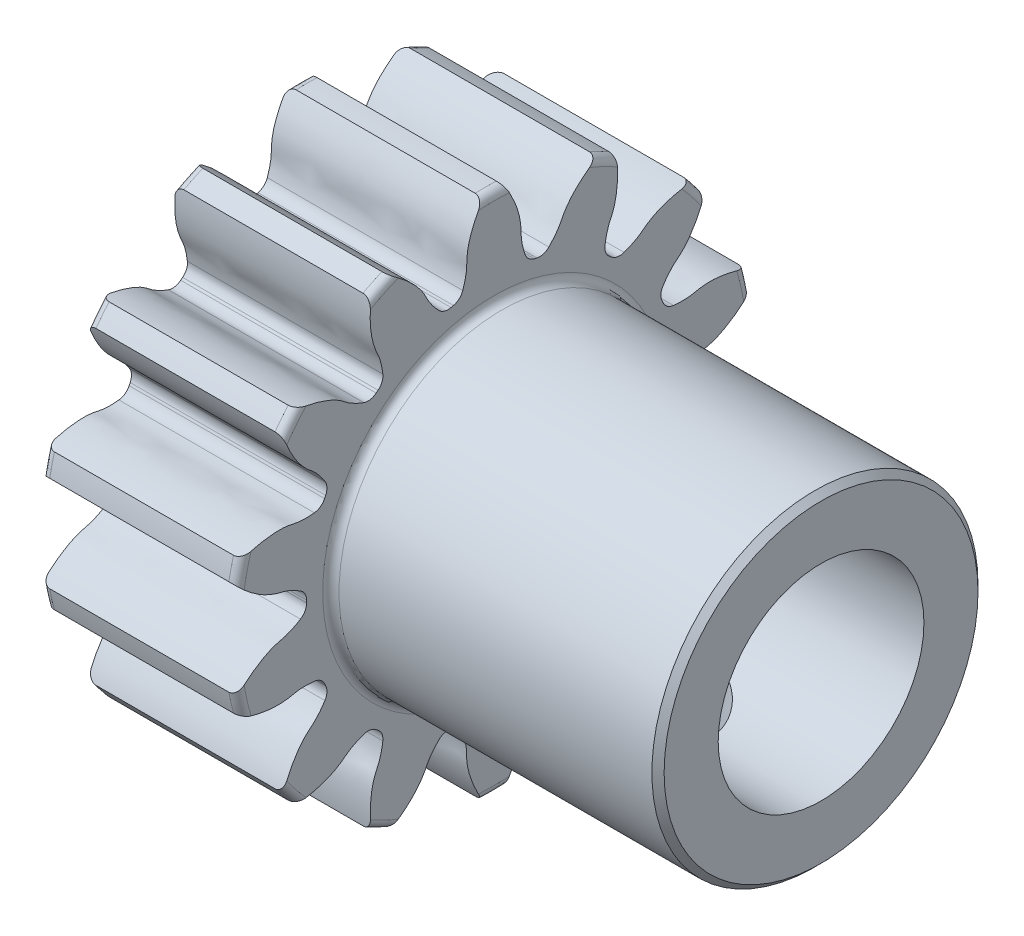
SolidWorks part; units mm, degrees
ref_plane "Front Plane" through (0, 0, 0) normal (0, 0, 1) x (1, 0, 0)
ref_plane "Top Plane" through (0, 0, 0) normal (0, 1, 0) x (1, 0, 0)
ref_plane "Right Plane" through (0, 0, 0) normal (1, 0, 0) x (0, 0, -1)
sketch "Sketch1" plane through (0, 0, 0) normal (0, 0, 1) x (1, 0, 0)
  line L0 (-2.3749, 6.35) -> (-2.3749, 0)
  line L1 (-2.3749, 0) -> (2.3749, 0)
  line L2 (2.3749, 0) -> (2.3749, 6.35)
  line L3 (2.3749, 6.35) -> (-2.3749, 6.35)
  line L4 (-2.3749, 0) -> (2.3749, 0) construction
revolve "Revolve1" add sketch "Sketch1" angle 360 about L4
sketch "Sketch2" plane through (2.3749, 0, 0) normal (1, 0, 0) x (0, 0, -1)
  arc A0 (2.522, 5.8277) -> (0.2563, 6.3448) centre (0, 0) ccw
  arc A1 (0.8169, 4.4791) -> (1.2074, 4.3899) centre (0, 0) cw
  spline S0 degree 3 poles (0.8169, 4.4791) (0.7969, 4.5356) (0.7764, 4.592) (0.7572, 4.6489) (0.7045, 4.8054) (0.6603, 4.9699) (0.6613, 5.1352) (0.6623, 5.3039) (0.6386, 5.4749) (0.5897, 5.6364) (0.537, 5.8109) (0.4638, 5.9799) (0.3768, 6.14) (0.339, 6.2096) (0.2987, 6.2779) (0.2563, 6.3448) knots -0.000178 -0.000178 -0.000178 -0.000178 0 0 0 0.000496 0.000496 0.000496 0.000997 0.000997 0.000997 0.001536 0.001536 0.001536 0.001769 0.001769 0.001769 0.001769
  spline S1 degree 3 poles (1.2074, 4.3899) (1.25, 4.4322) (1.2929, 4.4741) (1.3348, 4.517) (1.4503, 4.6352) (1.5615, 4.7642) (1.6323, 4.9135) (1.7046, 5.066) (1.8001, 5.2098) (1.9142, 5.3341) (2.0375, 5.4684) (2.1767, 5.5889) (2.3246, 5.6954) (2.3888, 5.7418) (2.4548, 5.7858) (2.522, 5.8277) knots -0.000178 -0.000178 -0.000178 -0.000178 0 0 0 0.000496 0.000496 0.000496 0.000997 0.000997 0.000997 0.001536 0.001536 0.001536 0.001769 0.001769 0.001769 0.001769
extrude "Cut-Extrude1" cut sketch "Sketch2" against normal through all
sketch "Sketch3" plane through (2.3749, 0, 0) normal (1, 0, 0) x (0, 0, -1)
  arc A0 (4.8008, 4.1563) -> (2.9838, 5.6053) centre (0, 0) ccw
  arc A1 (2.6794, 3.6811) -> (2.9926, 3.4313) centre (0, 0) cw
  spline S0 degree 3 poles (2.9838, 5.6053) (2.993, 5.5266) (2.9997, 5.4476) (3.0035, 5.3685) (3.0144, 5.1469) (2.9998, 4.9222) (2.9558, 4.7048) (2.9338, 4.596) (2.8984, 4.4887) (2.8487, 4.3895) (2.7829, 4.2582) (2.7401, 4.1143) (2.7155, 3.9695) (2.7093, 3.9331) (2.7039, 3.8966) (2.6993, 3.8599) (2.6919, 3.8004) (2.6859, 3.7407) (2.6794, 3.6811) knots -0.000236 -0.000236 -0.000236 -0.000236 0 0 0 0.000665 0.000665 0.000665 0.000998 0.000998 0.000998 0.00144 0.00144 0.00144 0.00155 0.00155 0.00155 0.001729 0.001729 0.001729 0.001729
  spline S1 degree 3 poles (2.9926, 3.4313) (3.0492, 3.451) (3.1061, 3.4701) (3.1625, 3.4905) (3.3178, 3.5469) (3.474, 3.6149) (3.6025, 3.7187) (3.7339, 3.8248) (3.8823, 3.9128) (4.0391, 3.9753) (4.2083, 4.0428) (4.3861, 4.091) (4.5655, 4.1228) (4.6435, 4.1367) (4.722, 4.1477) (4.8008, 4.1563) knots -0.000178 -0.000178 -0.000178 -0.000178 0 0 0 0.000496 0.000496 0.000496 0.000997 0.000997 0.000997 0.001536 0.001536 0.001536 0.001769 0.001769 0.001769 0.001769
extrude "Cut-Extrude2" cut sketch "Sketch3" against normal through all
sketch "Sketch4" plane through (2.3749, 0, 0) normal (1, 0, 0) x (0, 0, -1)
  arc A0 (6.1287, 1.6617) -> (5.1204, 3.7555) centre (0, 0) ccw
  arc A1 (4.0112, 2.154) -> (4.185, 1.7931) centre (0, 0) cw
  spline S0 degree 3 poles (5.1204, 3.7555) (5.0945, 3.6807) (5.0662, 3.6066) (5.0354, 3.5336) (4.949, 3.3293) (4.8383, 3.1332) (4.7044, 2.9564) (4.6374, 2.8679) (4.5589, 2.7866) (4.4711, 2.7188) (4.3548, 2.629) (4.2538, 2.518) (4.1688, 2.3982) (4.1475, 2.3681) (4.1268, 2.3375) (4.1068, 2.3065) (4.0742, 2.2561) (4.043, 2.2049) (4.0112, 2.154) knots -0.000236 -0.000236 -0.000236 -0.000236 0 0 0 0.000665 0.000665 0.000665 0.000998 0.000998 0.000998 0.00144 0.00144 0.00144 0.00155 0.00155 0.00155 0.001729 0.001729 0.001729 0.001729
  spline S1 degree 3 poles (4.185, 1.7931) (4.2446, 1.7862) (4.3041, 1.7787) (4.3638, 1.7727) (4.5282, 1.7561) (4.6984, 1.7496) (4.8593, 1.7874) (5.0236, 1.8259) (5.1955, 1.8408) (5.3639, 1.8292) (5.5457, 1.8165) (5.7267, 1.7828) (5.9022, 1.7336) (5.9785, 1.7123) (6.054, 1.6881) (6.1287, 1.6617) knots -0.000178 -0.000178 -0.000178 -0.000178 0 0 0 0.000496 0.000496 0.000496 0.000997 0.000997 0.000997 0.001536 0.001536 0.001536 0.001769 0.001769 0.001769 0.001769
extrude "Cut-Extrude3" cut sketch "Sketch4" against normal through all
sketch "Sketch5" plane through (2.3749, 0, 0) normal (1, 0, 0) x (0, 0, -1)
  arc A0 (6.2428, -1.162) -> (6.2428, 1.162) centre (0, 0) ccw
  arc A1 (4.5485, 0.2003) -> (4.5485, -0.2003) centre (0, 0) cw
  spline S0 degree 3 poles (6.2428, 1.162) (6.187, 1.1058) (6.1294, 1.0513) (6.0699, 0.9989) (5.9035, 0.8523) (5.7186, 0.7236) (5.5213, 0.6225) (5.4225, 0.5718) (5.3165, 0.5326) (5.2079, 0.5096) (5.0643, 0.4792) (4.9251, 0.4229) (4.7965, 0.3519) (4.7642, 0.334) (4.7323, 0.3155) (4.7008, 0.2962) (4.6496, 0.2649) (4.5993, 0.2323) (4.5485, 0.2003) knots -0.000236 -0.000236 -0.000236 -0.000236 0 0 0 0.000665 0.000665 0.000665 0.000998 0.000998 0.000998 0.00144 0.00144 0.00144 0.00155 0.00155 0.00155 0.001729 0.001729 0.001729 0.001729
  spline S1 degree 3 poles (4.5485, -0.2003) (4.5993, -0.2323) (4.6496, -0.2649) (4.7008, -0.2962) (4.8417, -0.3825) (4.9923, -0.4622) (5.1536, -0.498) (5.3183, -0.5345) (5.4797, -0.5957) (5.6263, -0.6793) (5.7847, -0.7695) (5.9331, -0.8785) (6.0699, -0.9989) (6.1294, -1.0513) (6.187, -1.1058) (6.2428, -1.162) knots -0.000178 -0.000178 -0.000178 -0.000178 0 0 0 0.000496 0.000496 0.000496 0.000997 0.000997 0.000997 0.001536 0.001536 0.001536 0.001769 0.001769 0.001769 0.001769
extrude "Cut-Extrude4" cut sketch "Sketch5" against normal through all
sketch "Sketch6" plane through (2.3749, 0, 0) normal (1, 0, 0) x (0, 0, -1)
  arc A0 (5.1204, -3.7555) -> (6.1287, -1.6617) centre (0, 0) ccw
  arc A1 (4.185, -1.7931) -> (4.0112, -2.154) centre (0, 0) cw
  spline S0 degree 3 poles (6.1287, -1.6617) (6.054, -1.6881) (5.9785, -1.7123) (5.9022, -1.7336) (5.6886, -1.7935) (5.4663, -1.8293) (5.2446, -1.8348) (5.1336, -1.8375) (5.0211, -1.8269) (4.9133, -1.8005) (4.7707, -1.7656) (4.6208, -1.7559) (4.4742, -1.7641) (4.4374, -1.7662) (4.4005, -1.769) (4.3638, -1.7727) (4.3041, -1.7787) (4.2446, -1.7862) (4.185, -1.7931) knots -0.000236 -0.000236 -0.000236 -0.000236 0 0 0 0.000665 0.000665 0.000665 0.000998 0.000998 0.000998 0.00144 0.00144 0.00144 0.00155 0.00155 0.00155 0.001729 0.001729 0.001729 0.001729
  spline S1 degree 3 poles (4.0112, -2.154) (4.043, -2.2049) (4.0742, -2.2561) (4.1068, -2.3065) (4.1963, -2.4454) (4.2973, -2.5825) (4.4271, -2.6847) (4.5597, -2.7892) (4.6786, -2.9143) (4.7744, -3.0532) (4.8779, -3.2032) (4.9644, -3.3658) (5.0354, -3.5336) (5.0662, -3.6066) (5.0945, -3.6807) (5.1204, -3.7555) knots -0.000178 -0.000178 -0.000178 -0.000178 0 0 0 0.000496 0.000496 0.000496 0.000997 0.000997 0.000997 0.001536 0.001536 0.001536 0.001769 0.001769 0.001769 0.001769
extrude "Cut-Extrude5" cut sketch "Sketch6" against normal through all
sketch "Sketch7" plane through (2.3749, 0, 0) normal (1, 0, 0) x (0, 0, -1)
  arc A0 (2.9838, -5.6053) -> (4.8008, -4.1563) centre (0, 0) ccw
  arc A1 (2.9926, -3.4313) -> (2.6794, -3.6811) centre (0, 0) cw
  spline S0 degree 3 poles (4.8008, -4.1563) (4.722, -4.1477) (4.6435, -4.1367) (4.5655, -4.1228) (4.3471, -4.0841) (4.1313, -4.0198) (3.9291, -3.9286) (3.8279, -3.8829) (3.7312, -3.8246) (3.6455, -3.754) (3.5322, -3.6606) (3.4014, -3.5869) (3.2657, -3.5307) (3.2316, -3.5166) (3.1972, -3.5031) (3.1625, -3.4905) (3.1061, -3.4701) (3.0492, -3.451) (2.9926, -3.4313) knots -0.000236 -0.000236 -0.000236 -0.000236 0 0 0 0.000665 0.000665 0.000665 0.000998 0.000998 0.000998 0.00144 0.00144 0.00144 0.00155 0.00155 0.00155 0.001729 0.001729 0.001729 0.001729
  spline S1 degree 3 poles (2.6794, -3.6811) (2.6859, -3.7407) (2.6919, -3.8004) (2.6993, -3.8599) (2.7197, -4.0239) (2.7513, -4.1913) (2.8239, -4.3397) (2.898, -4.4913) (2.9508, -4.6556) (2.9769, -4.8224) (3.005, -5.0024) (3.0124, -5.1864) (3.0035, -5.3685) (2.9997, -5.4476) (2.993, -5.5266) (2.9838, -5.6053) knots -0.000178 -0.000178 -0.000178 -0.000178 0 0 0 0.000496 0.000496 0.000496 0.000997 0.000997 0.000997 0.001536 0.001536 0.001536 0.001769 0.001769 0.001769 0.001769
extrude "Cut-Extrude6" cut sketch "Sketch7" against normal through all
sketch "Sketch8" plane through (2.3749, 0, 0) normal (1, 0, 0) x (0, 0, -1)
  arc A0 (0.2563, -6.3448) -> (2.522, -5.8277) centre (0, 0) ccw
  arc A1 (1.2074, -4.3899) -> (0.8169, -4.4791) centre (0, 0) cw
  spline S0 degree 3 poles (2.522, -5.8277) (2.4548, -5.7858) (2.3888, -5.7418) (2.3246, -5.6954) (2.1446, -5.5658) (1.978, -5.4142) (1.8354, -5.2443) (1.7641, -5.1593) (1.7023, -5.0647) (1.6557, -4.964) (1.5941, -4.8307) (1.5083, -4.7075) (1.4104, -4.598) (1.3858, -4.5704) (1.3606, -4.5434) (1.3348, -4.517) (1.2929, -4.4741) (1.25, -4.4322) (1.2074, -4.3899) knots -0.000236 -0.000236 -0.000236 -0.000236 0 0 0 0.000665 0.000665 0.000665 0.000998 0.000998 0.000998 0.00144 0.00144 0.00144 0.00155 0.00155 0.00155 0.001729 0.001729 0.001729 0.001729
  spline S1 degree 3 poles (0.8169, -4.4791) (0.7969, -4.5356) (0.7764, -4.592) (0.7572, -4.6489) (0.7045, -4.8054) (0.6603, -4.9699) (0.6613, -5.1352) (0.6623, -5.3039) (0.6386, -5.4749) (0.5897, -5.6364) (0.537, -5.8109) (0.4638, -5.9799) (0.3768, -6.14) (0.339, -6.2096) (0.2987, -6.2779) (0.2563, -6.3448) knots -0.000178 -0.000178 -0.000178 -0.000178 0 0 0 0.000496 0.000496 0.000496 0.000997 0.000997 0.000997 0.001536 0.001536 0.001536 0.001769 0.001769 0.001769 0.001769
extrude "Cut-Extrude7" cut sketch "Sketch8" against normal through all
sketch "Sketch9" plane through (2.3749, 0, 0) normal (1, 0, 0) x (0, 0, -1)
  arc A0 (-2.522, -5.8277) -> (-0.2563, -6.3448) centre (0, 0) ccw
  arc A1 (-0.8169, -4.4791) -> (-1.2074, -4.3899) centre (0, 0) cw
  spline S0 degree 3 poles (-0.2563, -6.3448) (-0.2987, -6.2779) (-0.339, -6.2096) (-0.3768, -6.14) (-0.4827, -5.9451) (-0.567, -5.7363) (-0.6217, -5.5213) (-0.6491, -5.4138) (-0.6638, -5.3018) (-0.662, -5.1908) (-0.6597, -5.0439) (-0.6836, -4.8957) (-0.7243, -4.7546) (-0.7345, -4.7191) (-0.7454, -4.6838) (-0.7572, -4.6489) (-0.7764, -4.592) (-0.7969, -4.5356) (-0.8169, -4.4791) knots -0.000236 -0.000236 -0.000236 -0.000236 0 0 0 0.000665 0.000665 0.000665 0.000998 0.000998 0.000998 0.00144 0.00144 0.00144 0.00155 0.00155 0.00155 0.001729 0.001729 0.001729 0.001729
  spline S1 degree 3 poles (-1.2074, -4.3899) (-1.25, -4.4322) (-1.2929, -4.4741) (-1.3348, -4.517) (-1.4503, -4.6352) (-1.5615, -4.7642) (-1.6323, -4.9135) (-1.7046, -5.066) (-1.8001, -5.2098) (-1.9142, -5.3341) (-2.0375, -5.4684) (-2.1767, -5.5889) (-2.3246, -5.6954) (-2.3888, -5.7418) (-2.4548, -5.7858) (-2.522, -5.8277) knots -0.000178 -0.000178 -0.000178 -0.000178 0 0 0 0.000496 0.000496 0.000496 0.000997 0.000997 0.000997 0.001536 0.001536 0.001536 0.001769 0.001769 0.001769 0.001769
extrude "Cut-Extrude8" cut sketch "Sketch9" against normal through all
sketch "Sketch10" plane through (2.3749, 0, 0) normal (1, 0, 0) x (0, 0, -1)
  arc A0 (-4.8008, -4.1563) -> (-2.9838, -5.6053) centre (0, 0) ccw
  arc A1 (-2.6794, -3.6811) -> (-2.9926, -3.4313) centre (0, 0) cw
  spline S0 degree 3 poles (-2.9838, -5.6053) (-2.993, -5.5266) (-2.9997, -5.4476) (-3.0035, -5.3685) (-3.0144, -5.1469) (-2.9998, -4.9222) (-2.9558, -4.7048) (-2.9338, -4.596) (-2.8984, -4.4887) (-2.8487, -4.3895) (-2.7829, -4.2582) (-2.7401, -4.1143) (-2.7155, -3.9695) (-2.7093, -3.9331) (-2.7039, -3.8966) (-2.6993, -3.8599) (-2.6919, -3.8004) (-2.6859, -3.7407) (-2.6794, -3.6811) knots -0.000236 -0.000236 -0.000236 -0.000236 0 0 0 0.000665 0.000665 0.000665 0.000998 0.000998 0.000998 0.00144 0.00144 0.00144 0.00155 0.00155 0.00155 0.001729 0.001729 0.001729 0.001729
  spline S1 degree 3 poles (-2.9926, -3.4313) (-3.0492, -3.451) (-3.1061, -3.4701) (-3.1625, -3.4905) (-3.3178, -3.5469) (-3.474, -3.6149) (-3.6025, -3.7187) (-3.7339, -3.8248) (-3.8823, -3.9128) (-4.0391, -3.9753) (-4.2083, -4.0428) (-4.3861, -4.091) (-4.5655, -4.1228) (-4.6435, -4.1367) (-4.722, -4.1477) (-4.8008, -4.1563) knots -0.000178 -0.000178 -0.000178 -0.000178 0 0 0 0.000496 0.000496 0.000496 0.000997 0.000997 0.000997 0.001536 0.001536 0.001536 0.001769 0.001769 0.001769 0.001769
extrude "Cut-Extrude9" cut sketch "Sketch10" against normal through all
sketch "Sketch11" plane through (2.3749, 0, 0) normal (1, 0, 0) x (0, 0, -1)
  arc A0 (-6.1287, -1.6617) -> (-5.1204, -3.7555) centre (0, 0) ccw
  arc A1 (-4.0112, -2.154) -> (-4.185, -1.7931) centre (0, 0) cw
  spline S0 degree 3 poles (-5.1204, -3.7555) (-5.0945, -3.6807) (-5.0662, -3.6066) (-5.0354, -3.5336) (-4.949, -3.3293) (-4.8383, -3.1332) (-4.7044, -2.9564) (-4.6374, -2.8679) (-4.5589, -2.7866) (-4.4711, -2.7188) (-4.3548, -2.629) (-4.2538, -2.518) (-4.1688, -2.3982) (-4.1475, -2.3681) (-4.1268, -2.3375) (-4.1068, -2.3065) (-4.0742, -2.2561) (-4.043, -2.2049) (-4.0112, -2.154) knots -0.000236 -0.000236 -0.000236 -0.000236 0 0 0 0.000665 0.000665 0.000665 0.000998 0.000998 0.000998 0.00144 0.00144 0.00144 0.00155 0.00155 0.00155 0.001729 0.001729 0.001729 0.001729
  spline S1 degree 3 poles (-4.185, -1.7931) (-4.2446, -1.7862) (-4.3041, -1.7787) (-4.3638, -1.7727) (-4.5282, -1.7561) (-4.6984, -1.7496) (-4.8593, -1.7874) (-5.0236, -1.8259) (-5.1955, -1.8408) (-5.3639, -1.8292) (-5.5457, -1.8165) (-5.7267, -1.7828) (-5.9022, -1.7336) (-5.9785, -1.7123) (-6.054, -1.6881) (-6.1287, -1.6617) knots -0.000178 -0.000178 -0.000178 -0.000178 0 0 0 0.000496 0.000496 0.000496 0.000997 0.000997 0.000997 0.001536 0.001536 0.001536 0.001769 0.001769 0.001769 0.001769
extrude "Cut-Extrude10" cut sketch "Sketch11" against normal through all
sketch "Sketch12" plane through (2.3749, 0, 0) normal (1, 0, 0) x (0, 0, -1)
  arc A0 (-6.2428, 1.162) -> (-6.2428, -1.162) centre (0, 0) ccw
  arc A1 (-4.5485, -0.2003) -> (-4.5485, 0.2003) centre (0, 0) cw
  spline S0 degree 3 poles (-6.2428, -1.162) (-6.187, -1.1058) (-6.1294, -1.0513) (-6.0699, -0.9989) (-5.9035, -0.8523) (-5.7186, -0.7236) (-5.5213, -0.6225) (-5.4225, -0.5718) (-5.3165, -0.5326) (-5.2079, -0.5096) (-5.0643, -0.4792) (-4.9251, -0.4229) (-4.7965, -0.3519) (-4.7642, -0.334) (-4.7323, -0.3155) (-4.7008, -0.2962) (-4.6496, -0.2649) (-4.5993, -0.2323) (-4.5485, -0.2003) knots -0.000236 -0.000236 -0.000236 -0.000236 0 0 0 0.000665 0.000665 0.000665 0.000998 0.000998 0.000998 0.00144 0.00144 0.00144 0.00155 0.00155 0.00155 0.001729 0.001729 0.001729 0.001729
  spline S1 degree 3 poles (-4.5485, 0.2003) (-4.5993, 0.2323) (-4.6496, 0.2649) (-4.7008, 0.2962) (-4.8417, 0.3825) (-4.9923, 0.4622) (-5.1536, 0.498) (-5.3183, 0.5345) (-5.4797, 0.5957) (-5.6263, 0.6793) (-5.7847, 0.7695) (-5.9331, 0.8785) (-6.0699, 0.9989) (-6.1294, 1.0513) (-6.187, 1.1058) (-6.2428, 1.162) knots -0.000178 -0.000178 -0.000178 -0.000178 0 0 0 0.000496 0.000496 0.000496 0.000997 0.000997 0.000997 0.001536 0.001536 0.001536 0.001769 0.001769 0.001769 0.001769
extrude "Cut-Extrude11" cut sketch "Sketch12" against normal through all
sketch "Sketch13" plane through (2.3749, 0, 0) normal (1, 0, 0) x (0, 0, -1)
  arc A0 (-5.1204, 3.7555) -> (-6.1287, 1.6617) centre (0, 0) ccw
  arc A1 (-4.185, 1.7931) -> (-4.0112, 2.154) centre (0, 0) cw
  spline S0 degree 3 poles (-6.1287, 1.6617) (-6.054, 1.6881) (-5.9785, 1.7123) (-5.9022, 1.7336) (-5.6886, 1.7935) (-5.4663, 1.8293) (-5.2446, 1.8348) (-5.1336, 1.8375) (-5.0211, 1.8269) (-4.9133, 1.8005) (-4.7707, 1.7656) (-4.6208, 1.7559) (-4.4742, 1.7641) (-4.4374, 1.7662) (-4.4005, 1.769) (-4.3638, 1.7727) (-4.3041, 1.7787) (-4.2446, 1.7862) (-4.185, 1.7931) knots -0.000236 -0.000236 -0.000236 -0.000236 0 0 0 0.000665 0.000665 0.000665 0.000998 0.000998 0.000998 0.00144 0.00144 0.00144 0.00155 0.00155 0.00155 0.001729 0.001729 0.001729 0.001729
  spline S1 degree 3 poles (-4.0112, 2.154) (-4.043, 2.2049) (-4.0742, 2.2561) (-4.1068, 2.3065) (-4.1963, 2.4454) (-4.2973, 2.5825) (-4.4271, 2.6847) (-4.5597, 2.7892) (-4.6786, 2.9143) (-4.7744, 3.0532) (-4.8779, 3.2032) (-4.9644, 3.3658) (-5.0354, 3.5336) (-5.0662, 3.6066) (-5.0945, 3.6807) (-5.1204, 3.7555) knots -0.000178 -0.000178 -0.000178 -0.000178 0 0 0 0.000496 0.000496 0.000496 0.000997 0.000997 0.000997 0.001536 0.001536 0.001536 0.001769 0.001769 0.001769 0.001769
extrude "Cut-Extrude12" cut sketch "Sketch13" against normal through all
sketch "Sketch14" plane through (2.3749, 0, 0) normal (1, 0, 0) x (0, 0, -1)
  arc A0 (-2.9838, 5.6053) -> (-4.8008, 4.1563) centre (0, 0) ccw
  arc A1 (-2.9926, 3.4313) -> (-2.6794, 3.6811) centre (0, 0) cw
  spline S0 degree 3 poles (-4.8008, 4.1563) (-4.722, 4.1477) (-4.6435, 4.1367) (-4.5655, 4.1228) (-4.3471, 4.0841) (-4.1313, 4.0198) (-3.9291, 3.9286) (-3.8279, 3.8829) (-3.7312, 3.8246) (-3.6455, 3.754) (-3.5322, 3.6606) (-3.4014, 3.5869) (-3.2657, 3.5307) (-3.2316, 3.5166) (-3.1972, 3.5031) (-3.1625, 3.4905) (-3.1061, 3.4701) (-3.0492, 3.451) (-2.9926, 3.4313) knots -0.000236 -0.000236 -0.000236 -0.000236 0 0 0 0.000665 0.000665 0.000665 0.000998 0.000998 0.000998 0.00144 0.00144 0.00144 0.00155 0.00155 0.00155 0.001729 0.001729 0.001729 0.001729
  spline S1 degree 3 poles (-2.6794, 3.6811) (-2.6859, 3.7407) (-2.6919, 3.8004) (-2.6993, 3.8599) (-2.7197, 4.0239) (-2.7513, 4.1913) (-2.8239, 4.3397) (-2.898, 4.4913) (-2.9508, 4.6556) (-2.9769, 4.8224) (-3.005, 5.0024) (-3.0124, 5.1864) (-3.0035, 5.3685) (-2.9997, 5.4476) (-2.993, 5.5266) (-2.9838, 5.6053) knots -0.000178 -0.000178 -0.000178 -0.000178 0 0 0 0.000496 0.000496 0.000496 0.000997 0.000997 0.000997 0.001536 0.001536 0.001536 0.001769 0.001769 0.001769 0.001769
extrude "Cut-Extrude13" cut sketch "Sketch14" against normal through all
sketch "Sketch15" plane through (2.3749, 0, 0) normal (1, 0, 0) x (0, 0, -1)
  arc A0 (-0.2563, 6.3448) -> (-2.522, 5.8277) centre (0, 0) ccw
  arc A1 (-1.2074, 4.3899) -> (-0.8169, 4.4791) centre (0, 0) cw
  spline S0 degree 3 poles (-2.522, 5.8277) (-2.4548, 5.7858) (-2.3888, 5.7418) (-2.3246, 5.6954) (-2.1446, 5.5658) (-1.978, 5.4142) (-1.8354, 5.2443) (-1.7641, 5.1593) (-1.7023, 5.0647) (-1.6557, 4.964) (-1.5941, 4.8307) (-1.5083, 4.7075) (-1.4104, 4.598) (-1.3858, 4.5704) (-1.3606, 4.5434) (-1.3348, 4.517) (-1.2929, 4.4741) (-1.25, 4.4322) (-1.2074, 4.3899) knots -0.000236 -0.000236 -0.000236 -0.000236 0 0 0 0.000665 0.000665 0.000665 0.000998 0.000998 0.000998 0.00144 0.00144 0.00144 0.00155 0.00155 0.00155 0.001729 0.001729 0.001729 0.001729
  spline S1 degree 3 poles (-0.8169, 4.4791) (-0.7969, 4.5356) (-0.7764, 4.592) (-0.7572, 4.6489) (-0.7045, 4.8054) (-0.6603, 4.9699) (-0.6613, 5.1352) (-0.6623, 5.3039) (-0.6386, 5.4749) (-0.5897, 5.6364) (-0.537, 5.8109) (-0.4638, 5.9799) (-0.3768, 6.14) (-0.339, 6.2096) (-0.2987, 6.2779) (-0.2563, 6.3448) knots -0.000178 -0.000178 -0.000178 -0.000178 0 0 0 0.000496 0.000496 0.000496 0.000997 0.000997 0.000997 0.001536 0.001536 0.001536 0.001769 0.001769 0.001769 0.001769
extrude "Cut-Extrude14" cut sketch "Sketch15" against normal through all
sketch "Sketch16" plane through (0, 0, 0) normal (0, 0, 1) x (1, 0, 0)
  line L0 (2.3749, 3.9624) -> (2.3749, 0)
  line L1 (2.3749, 0) -> (10.3251, 0)
  line L2 (10.3251, 0) -> (10.3251, 3.9624)
  line L3 (10.3251, 3.9624) -> (2.3749, 3.9624)
  line L4 (2.3749, 0) -> (10.3251, 0) construction
revolve "Revolve2" add sketch "Sketch16" angle 360 about L4
hole_wizard "M3.5 Clearance Hole1" positions "Sketch18" profile "Sketch17" hole size "M3.5" standard "ANSI Metric"
sketch "Sketch18" plane through (10.3251, 0, 0) normal (1, 0, 0) x (0, 0, -1)
  point P0 (0, 0)
sketch "Sketch17" plane through (10.3251, 0, 0) normal (0, 1, 0) x (0, 0, -1)
  line L0 (0, 0) -> (0, 12.7)
  line L1 (0, 12.7) -> (1.9812, 12.7)
  line L2 (1.9812, 12.7) -> (1.9812, 0)
  line L5 (1.9812, 0) -> (0, 0)
  line L11 (0, -6.35) -> (0, 107.95) construction
  dimension "Thru Hole Dia." = 3.9624
  dimension "Thru Hole Depth" = 12.7
chamfer "Chamfer1" distance 0.1486 angle 45 3 edges at (-2.3749, 0, -1.9812) (10.3251, 0, -3.9624) (10.3251, 0, -1.9812)
fillet "Fillet1" radius 0.1984 29 edges at (-2.3749, 6.35, 0) (2.3749, -5.7212, -2.7552) (2.3749, -1.413, 6.1908) (-2.3749, 5.7212, 2.7552) (2.3749, 3.9592, -4.9646) (-2.3749, 3.9592, 4.9646) (2.3749, 3.9592, 4.9646) (-2.3749, 1.413, 6.1908) (2.3749, -5.7212, 2.7552) (-2.3749, -1.413, 6.1908) (2.3749, -1.413, -6.1908) (-2.3749, -3.9592, 4.9646) (2.3749, 0, -3.9624) (-2.3749, -5.7212, 2.7552) (2.3749, 5.7212, 2.7552) (-2.3749, -6.35, 0) (2.3749, 1.413, 6.1908) (-2.3749, -5.7212, -2.7552) (2.3749, -3.9592, 4.9646) (-2.3749, -3.9592, -4.9646) (2.3749, -6.35, 0) (-2.3749, -1.413, -6.1908) (2.3749, -3.9592, -4.9646) (-2.3749, 1.413, -6.1908) (2.3749, 1.413, -6.1908) (-2.3749, 3.9592, -4.9646) (2.3749, 5.7212, -2.7552) (2.3749, 6.35, 0) (-2.3749, 5.7212, -2.7552)
fillet "Fillet2" radius 0.3096 28 edges at (0, -0.2003, -4.5485) (0, 3.4313, -2.9926) (0, 1.7931, -4.185) (0, -4.4791, 0.8169) (0, 4.4791, -0.8169) (0, -4.3899, 1.2074) (0, 1.7931, 4.185) (0, -4.4791, -0.8169) (0, 3.4313, 2.9926) (0, -4.3899, -1.2074) (0, 4.3899, 1.2074) (0, -3.6811, 2.6794) (0, 0.2003, 4.5485) (0, -3.4313, 2.9926) (0, 0.2003, -4.5485) (0, -3.6811, -2.6794) (0, 2.154, 4.0112) (0, -3.4313, -2.9926) (0, 2.154, -4.0112) (0, -2.154, 4.0112) (0, 3.6811, 2.6794) (0, -1.7931, 4.185) (0, 3.6811, -2.6794) (0, -2.154, -4.0112) (0, 4.4791, 0.8169) (0, -1.7931, -4.185) (0, -0.2003, 4.5485) (0, 4.3899, -1.2074)
sketch "Sketch19" plane through (10.3251, 0, 0) normal (1, 0, 0) x (0, 0, -1)
  circle A0 centre (0, 0) radius 2.5
  dimension "D1" = 5
extrude "Shaft widening" cut sketch "Sketch19" against normal through all
sketch "Sketch20" plane through (0, 0, 0) normal (0, 1, 0) x (1, 0, 0)
  line L0 (10.1765, 3.9624) -> (10.1765, -3.9624) construction
  line L1 (10.1765, 3.9624) -> (10.1765, -3.9624) construction
  line L2 (10.1765, 0) -> (2.5733, 0) construction
  line L3 (2.5733, 3.9624) -> (2.5733, -3.9624) construction
  circle A0 centre (6.3749, 0) radius 1.27
  dimension "D1" = 2.54
extrude "Set screw hole" cut sketch "Sketch20" against normal through all
